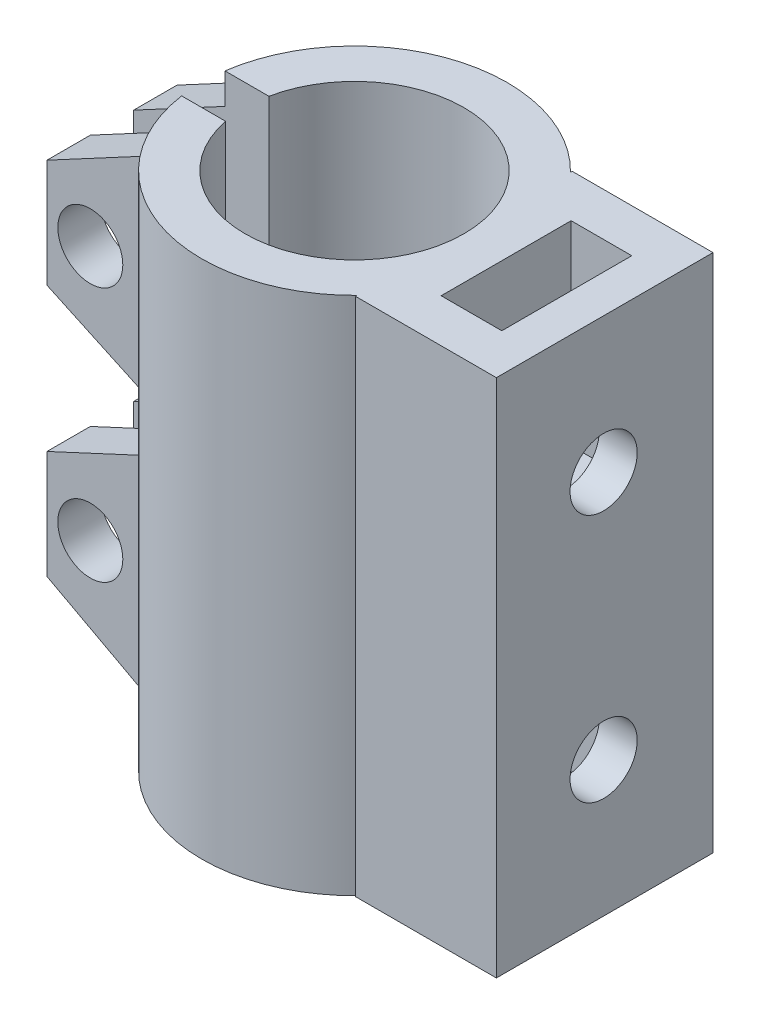
SolidWorks part; units mm, degrees
ref_plane "Front Plane" through (0, 0, 0) normal (0, 0, 1) x (1, 0, 0)
ref_plane "Top Plane" through (0, 0, 0) normal (0, 1, 0) x (1, 0, 0)
ref_plane "Right Plane" through (0, 0, 0) normal (1, 0, 0) x (0, 0, -1)
sketch "Sketch1" plane through (0, 0, 0) normal (0, 0, 1) x (1, 0, 0)
  line L0 (-0.1104, 2.9584) -> (-0.1104, -3.2034) construction
  line L1 (-2.6604, -21.0416) -> (-7.1604, -21.0416)
  line L2 (-5.1604, 2.9584) -> (-5.1604, -11.0416)
  line L3 (-5.1604, -11.0416) -> (-2.6604, -11.0416)
  line L4 (-2.6604, -11.0416) -> (-2.6604, -21.0416)
  line L5 (-7.1604, -21.0416) -> (-7.1604, 2.9584)
  line L6 (-7.1604, 2.9584) -> (-5.1604, 2.9584)
  dimension "D1" = 5.05
  dimension "D2" = 2.55
  dimension "D3" = 2
  dimension "D4" = 14
  dimension "D5" = 10
revolve "Revolve1" add sketch "Sketch1" angle 360 about L0
sketch "Sketch2" plane through (0, 2.9584, 0) normal (0, 1, 0) x (1, 0, 0)
  line L1 (-8.5733, 1) -> (-1.7475, 1)
  line L2 (-8.5733, 1) -> (-8.5733, -1)
  line L3 (-8.5733, -1) -> (-1.7475, -1)
  line L4 (-1.7475, 1) -> (-1.7475, -1)
  line L5 (-8.5733, 1) -> (-1.7475, -1) construction
  line L6 (-8.5733, -1) -> (-1.7475, 1) construction
  circle A0 centre (-0.1104, 0) radius 5.05 construction
  circle A1 centre (-0.1104, 0) radius 5.05 construction
  point P0 (-5.1604, 0)
  dimension "D1" = 2
extrude "Cut-Extrude1" cut sketch "Sketch2" against normal through all
sketch "Sketch3" plane through (0, 0, -1) normal (0, 0, 1) x (1, 0, 0)
  line L0 (-6.3059, 1.9584) -> (-11.3059, -0.7195)
  line L1 (-11.3059, -0.7195) -> (-11.3059, -5.7195)
  line L2 (-11.3059, -5.7195) -> (-6.3059, -8.0416)
  line L3 (-6.3059, -8.0416) -> (-6.3059, 1.9584)
  line L4 (-5.0604, 2.9584) -> (-7.0892, 2.9584) construction
  circle A0 centre (-9.3059, -3.1577) radius 1.5
  dimension "D5" = 3
  dimension "D1" = 5
  dimension "D2" = 10
  dimension "D3" = 1
  dimension "D4" = 5
  dimension "D6" = 2
extrude "Boss-Extrude1" add sketch "Sketch3" against normal blind 2
ref_plane "Plane1" through (0, 0, 0) normal (0, 0, 1) x (1, 0, 0)
mirror "Mirror1" about plane through (0, 0, 0) normal (0, 0, 1) of "Boss-Extrude1"
sketch "Sketch4" plane through (0, 2.9584, 0) normal (0, 1, 0) x (1, 0, 0)
  line L1 (4.9396, 5) -> (11.4396, 5)
  line L2 (4.9396, 5) -> (4.9396, -5)
  line L3 (4.9396, -5) -> (11.4396, -5)
  line L4 (11.4396, 5) -> (11.4396, -5)
  arc A2 (-5.0604, -1) -> (-5.0604, 1) centre (-0.1104, 0) ccw construction
  dimension "D1" = 10
  dimension "D2" = 5
  dimension "D3" = 6.5
extrude "Boss-Extrude2" add sketch "Sketch4" against normal through all
sketch "Sketch5" plane through (0, 2.9584, 0) normal (0, 1, 0) x (1, 0, 0)
  line L1 (6.8896, 3) -> (9.6896, 3)
  line L2 (6.8896, 3) -> (6.8896, -3)
  line L3 (6.8896, -3) -> (9.6896, -3)
  line L4 (9.6896, 3) -> (9.6896, -3)
  line L5 (6.8896, 3) -> (9.6896, -3) construction
  line L6 (6.8896, -3) -> (9.6896, 3) construction
  arc A0 (-5.0604, -1) -> (-5.0604, 1) centre (-0.1104, 0) ccw construction
  point P0 (8.2896, 0)
  dimension "2,8" = 2.8
  dimension "D2" = 6
  dimension "D3" = 7
extrude "Cut-Extrude2" cut sketch "Sketch5" against normal blind 9
ref_plane "Plane2" through (0, -9.0416, 0) normal (0, 1, 0) x (1, 0, 0)
mirror "Mirror2" about plane through (0, -9.0416, 0) normal (0, 1, 0) of "Cut-Extrude2"
sketch "Sketch6" plane through (11.4396, 0, 0) normal (1, 0, 0) x (0, 0, -1)
  line L0 (7.755, -9.0416) -> (-7.755, -9.0416) construction
  line L1 (-7.05, 2.9584) -> (-7.05, -21.0416) construction
  circle A0 centre (-0.05, -3.2916) radius 1.55
  dimension "D1" = 3.1
  dimension "D2" = 7
  dimension "D3" = 5.75
extrude "Cut-Extrude3" cut sketch "Sketch6" against normal blind 10
mirror "Mirror3" about plane through (0, -9.0416, 0) normal (0, 1, 0) of "Cut-Extrude3"
mirror "Mirror4" about plane through (0, -9.0416, 0) normal (0, 1, 0) of "Mirror1", "Boss-Extrude1"
